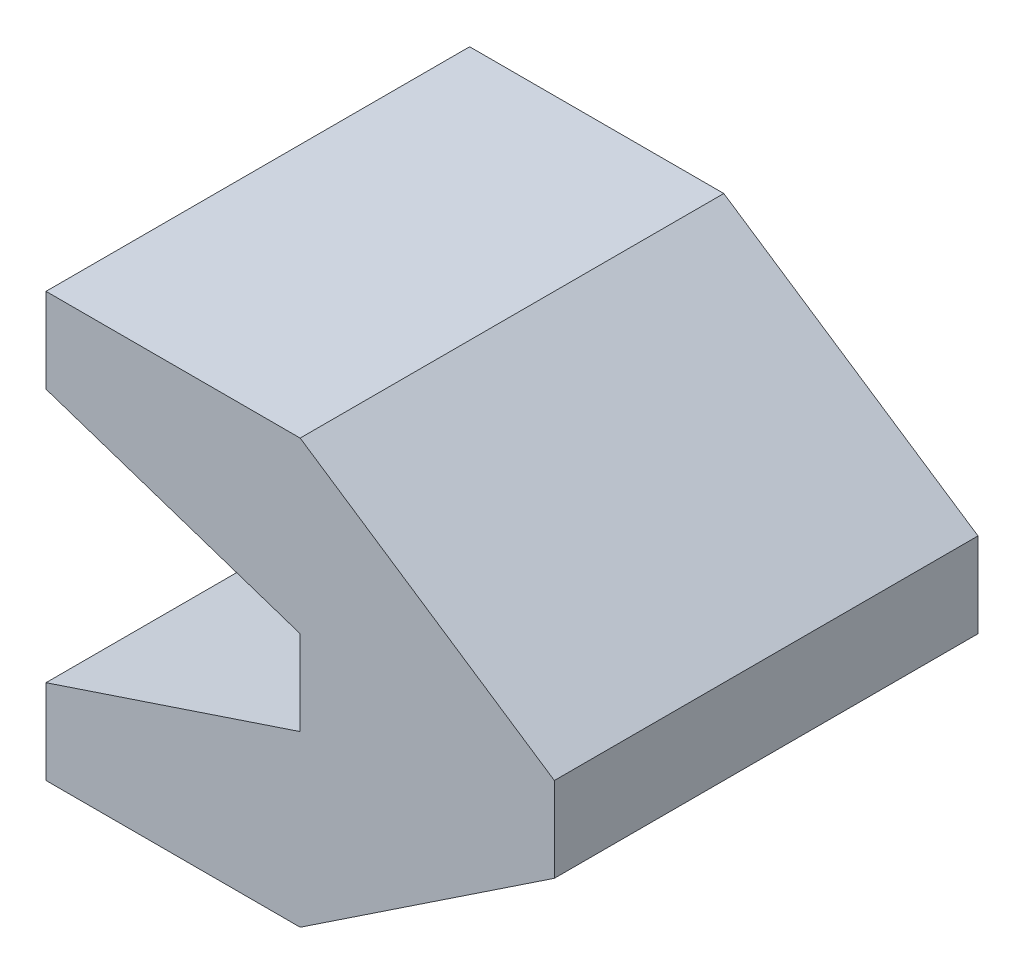
SolidWorks part; units mm, degrees
ref_plane "Front Plane" through (0, 0, 0) normal (0, 0, 1) x (1, 0, 0)
ref_plane "Top Plane" through (0, 0, 0) normal (0, 1, 0) x (1, 0, 0)
ref_plane "Right Plane" through (0, 0, 0) normal (1, 0, 0) x (0, 0, -1)
sketch "Sketch1" plane through (0, 0, 0) normal (0, 0, 1) x (1, 0, 0)
  line L0 (-15, 25) -> (0, 25)
  line L1 (0, 25) -> (15, 15)
  line L2 (15, 15) -> (15, 10)
  line L3 (15, 10) -> (0, 0)
  line L4 (0, 0) -> (-15, 0)
  line L5 (-15, 0) -> (-15, 5)
  line L6 (-15, 5) -> (0, 10)
  line L7 (0, 10) -> (0, 15)
  line L8 (0, 15) -> (-15, 20)
  line L9 (-15, 20) -> (-15, 25)
  point P5 (0, 15)
  point P11 (15, 0)
  point P12 (-15, 15)
  point P13 (-15, 10)
  dimension "D1" = 15
  dimension "D2" = 5
  dimension "D3" = 5
  dimension "D4" = 5
  dimension "D5" = 5
  dimension "D6" = 15
  dimension "D7" = 15
  dimension "D8" = 10
  dimension "D9" = 15
  dimension "D10" = 10
  dimension "D11" = 15
  dimension "D12" = 5
  dimension "D13" = 15
  dimension "D14" = 5
  dimension "D15" = 15
extrude "Boss-Extrude1" add sketch "Sketch1" along normal blind 25
